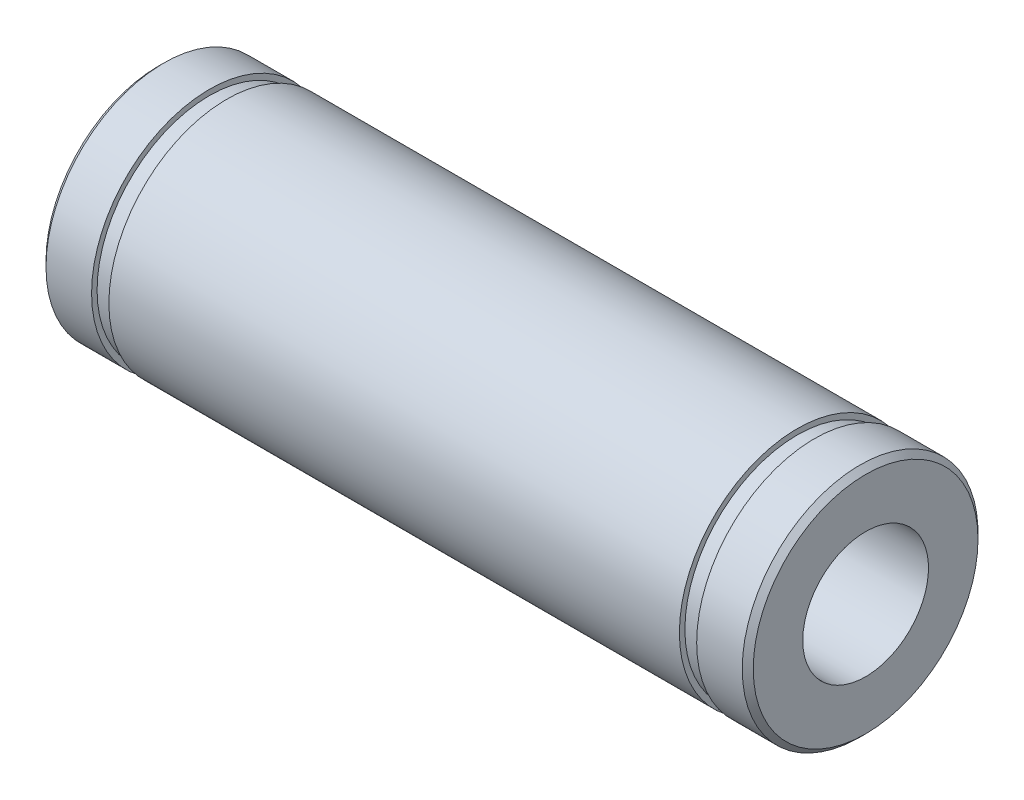
SolidWorks part; units mm, degrees
material "Легированная сталь"
ref_plane "Спереди" through (0, 0, 0) normal (0, 0, 1) x (1, 0, 0)
ref_plane "Сверху" through (0, 0, 0) normal (0, 1, 0) x (1, 0, 0)
ref_plane "Справа" through (0, 0, 0) normal (1, 0, 0) x (0, 0, -1)
other "Configuration Table"
sketch "Эскиз1" plane through (0, 0, 0) normal (0, 1, 0) x (1, 0, 0)
  line L0 (-14.548, 0) -> (15.9128, 0) construction
  line L1 (-11.65, -7.5) -> (-8.75, -7.5)
  line L2 (-12, -7.15) -> (-12, -4)
  line L4 (33, -7.15) -> (33, -4)
  line L5 (-12, -4) -> (33, -4)
  line L6 (-7.65, -7.5) -> (28.65, -7.5)
  line L7 (-8.75, -7.15) -> (-7.65, -7.15)
  line L8 (-7.65, -7.15) -> (-7.65, -7.5)
  line L9 (-8.75, -7.15) -> (-8.75, -7.5)
  line L10 (29.75, -7.5) -> (29.75, -7.15)
  line L11 (29.75, -7.15) -> (28.65, -7.15)
  line L12 (28.65, -7.15) -> (28.65, -7.5)
  line L13 (10.5, 0) -> (10.5, -9.4202) construction
  line L15 (29.75, -7.5) -> (32.65, -7.5)
  line L16 (-12, -7.15) -> (-11.65, -7.5)
  line L17 (33, -7.15) -> (32.65, -7.5)
  point P0 (0, 0)
  point P1 (-8.2, -7.15)
  dimension "D2" = 135
  dimension "D3" = 1.1
  dimension "D4" = 22.5
  dimension "D5" = 1.1
  dimension "D6" = 7.15
  dimension "D7" = 7.15
  dimension "D8" = 0.495
  dimension "D9" = 3.15
  dimension "D11" = 135
  dimension "D12" = 2.9
revolve "Повернуть1" add sketch "Эскиз1" angle 360 about L0
